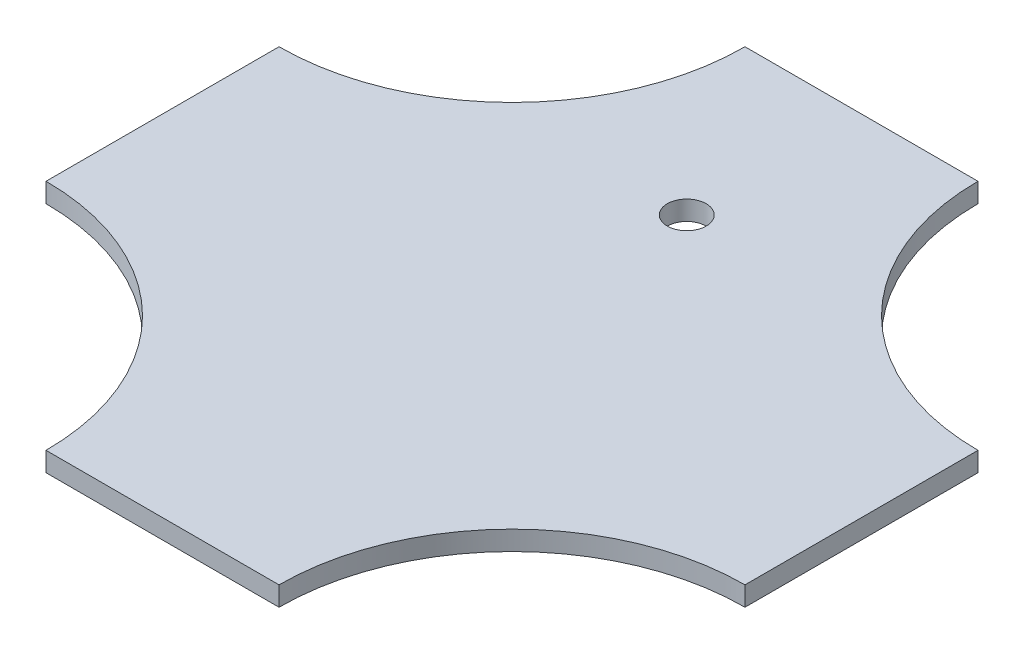
SolidWorks part; units mm, degrees
ref_plane "Front Plane" through (0, 0, 0) normal (0, 0, 1) x (1, 0, 0)
ref_plane "Top Plane" through (0, 0, 0) normal (0, 1, 0) x (1, 0, 0)
ref_plane "Right Plane" through (0, 0, 0) normal (1, 0, 0) x (0, 0, -1)
sketch "Sketch1" plane through (0, 0, 0) normal (0, 1, 0) x (1, 0, 0)
  line L0 (215.4305, 862.1306) -> (1077.1523, 862.1306) construction
  line L1 (-60, -60) -> (-60, -180)
  line L2 (60, 180) -> (-60, 180)
  line L3 (60, 180) -> (60, 60)
  line L4 (60, -180) -> (-60, -180)
  line L5 (-60, 180) -> (-60, 60)
  line L6 (-180, 60) -> (-60, 60)
  line L7 (-180, 60) -> (-180, -60)
  line L8 (-180, -60) -> (-60, -60)
  line L9 (180, 60) -> (180, -60)
  line L10 (60, -60) -> (60, -180)
  line L11 (60, 60) -> (180, 60)
  line L12 (60, -60) -> (180, -60)
  line L13 (-180, 60) -> (-180, 180) construction
  line L14 (-180, 180) -> (-60, 180) construction
  line L15 (0, 180) -> (0, -180) construction
  line L16 (-180, 0) -> (180, 0) construction
  arc A0 (-60, 180) -> (-180, 60) centre (-180, 180) cw
  arc A1 (60, 180) -> (180, 60) centre (180, 180) ccw
  arc A2 (180, -60) -> (60, -180) centre (180, -180) ccw
  arc A3 (-180, -60) -> (-60, -180) centre (-180, -180) cw
  point P19 (-180, 0)
  point P23 (0, 0)
  dimension "D1" = 120
  dimension "D2" = 180
extrude "Boss-Extrude1" add sketch "Sketch1" along normal blind 10 contours L10 L12 L9 L11 L3 L2 L5 L6 L7 L8 L1 L4 | L5 A0 L6 | A1 L3 L11 | A2 L12 L10 | L8 A3 L1
sketch "Sketch2" plane through (0, 0, 0) normal (0, -1, 0) x (1, 0, 0)
  line L0 (0, -180) -> (0, 0) construction
  line L1 (60, -180) -> (-60, -180) construction
  circle A0 centre (0, -90) radius 10
  dimension "D1" = 20
extrude "Cut-Extrude1" cut sketch "Sketch2" against normal up to surface (10 mm away) up to face at (0, 10, 0)
sketch "Sketch5" plane through (0, 0, 0) normal (0, -1, 0) x (1, 0, 0)
  line L0 (-24.5, -110) -> (-28.5, -110) construction
  line L1 (28.5, -110) -> (24.5, -110) construction
  line L2 (-24.5, -110) -> (-28.5, -110)
  line L3 (28.5, -110) -> (24.5, -110)
  line L5 (28.5, -110) -> (-28.5, -110)
  line L6 (28.5, -110) -> (28.5, -114)
  line L7 (28.5, -114) -> (-28.5, -114)
  line L8 (-28.5, -110) -> (-28.5, -114)
  point P7 (0, 0)
  dimension "D1" = 4
extrude "Cut-Extrude3" cut sketch "Sketch5" against normal blind 4 contours L2 L8 L7 L6 L3 L5
